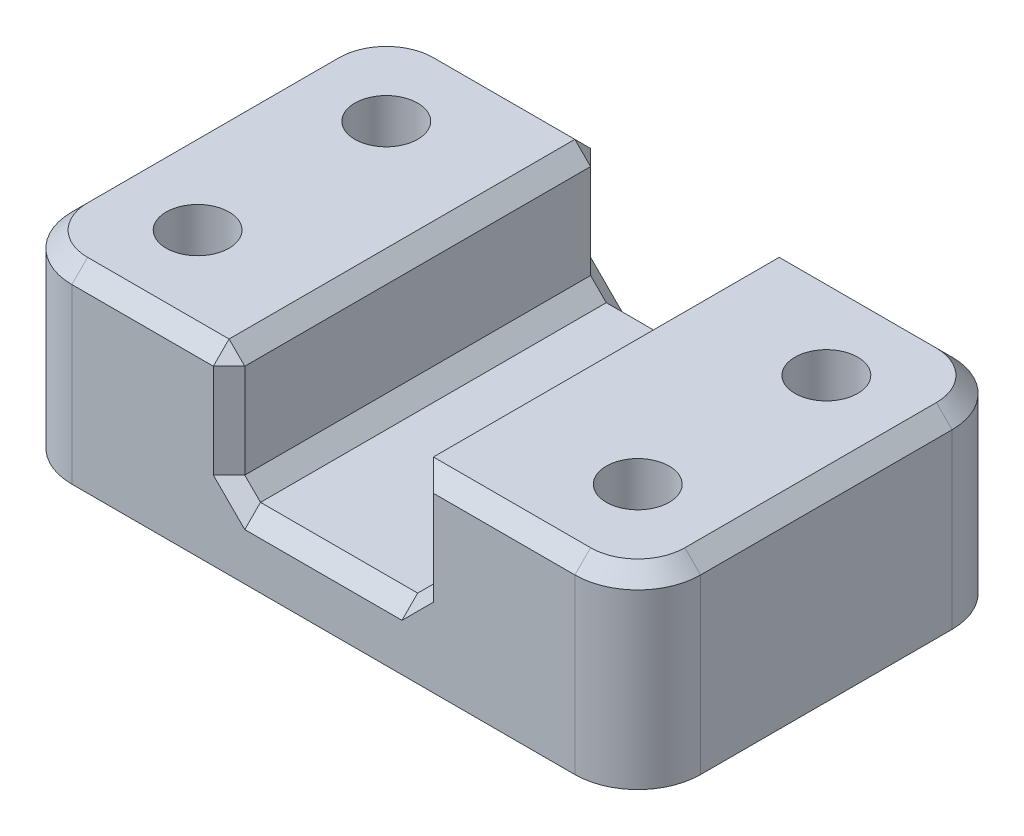
SolidWorks part; units mm, degrees
ref_plane "Front Plane" through (0, 0, 0) normal (0, 0, 1) x (1, 0, 0)
ref_plane "Top Plane" through (0, 0, 0) normal (0, 1, 0) x (1, 0, 0)
ref_plane "Right Plane" through (0, 0, 0) normal (1, 0, 0) x (0, 0, -1)
sketch "Sketch2" plane through (0, 0, 0) normal (0, 1, 0) x (1, 0, 0)
  line L0 (0, 23.318) -> (0, 0) construction
  line L1 (-63.5, -38.1) -> (63.5, -38.1)
  line L2 (-63.5, -38.1) -> (-63.5, 38.1)
  line L3 (-63.5, 38.1) -> (63.5, 38.1)
  line L4 (63.5, -38.1) -> (63.5, 38.1)
  line L5 (-63.5, -38.1) -> (63.5, 38.1) construction
  line L6 (-63.5, 38.1) -> (63.5, -38.1) construction
  line L7 (0, 0) -> (-53.7148, 0) construction
  circle A0 centre (-44.45, 19.05) radius 6.35
  circle A1 centre (44.45, 19.05) radius 6.35
  circle A2 centre (-44.45, -19.05) radius 6.35
  circle A3 centre (44.45, -19.05) radius 6.35
  point P0 (0, 0)
  dimension "D3" = 12.7
  dimension "D1" = 127
  dimension "D2" = 76.2
  dimension "D4" = 19.05
  dimension "D5" = 19.05
extrude "Boss-Extrude1" add sketch "Sketch2" along normal blind 38.1
sketch "Sketch3" plane through (0, 38.1, 0) normal (0, 1, 0) x (1, 0, 0)
  line L0 (63.5, 38.1) -> (-63.5, 38.1) construction
  line L1 (-19.05, -38.1) -> (19.05, -38.1)
  line L2 (-19.05, -38.1) -> (-19.05, 38.1)
  line L3 (-19.05, 38.1) -> (19.05, 38.1)
  line L4 (19.05, -38.1) -> (19.05, 38.1)
  line L5 (-19.05, -38.1) -> (19.05, 38.1) construction
  line L6 (-19.05, 38.1) -> (19.05, -38.1) construction
  point P0 (0, 0)
  point P8 (0, 0)
  point P9 (0, 0)
  dimension "D1" = 38.1
extrude "Cut-Extrude2" cut sketch "Sketch3" against normal blind 25.4 contours L2 L1 L4 L3
fillet "Fillet1" radius 12.7 4 edges at (-63.5, 19.05, -38.1) (-63.5, 19.05, 38.1) (63.5, 19.05, -38.1) (63.5, 19.05, 38.1)
chamfer "Chamfer1" distance 3.175 angle 45 19 edges at (-19.05, 38.1, 0) (-34.925, 38.1, 38.1) (-59.7803, 38.1, 34.3803) (-63.5, 38.1, 0) (-59.7803, 38.1, -34.3803) (-34.925, 38.1, -38.1) (19.05, 25.4, 38.1) (19.05, 25.4, -38.1) (-19.05, 25.4, 38.1) (-19.05, 25.4, -38.1) (19.05, 12.7, 0) (0, 12.7, 38.1) (-19.05, 12.7, 0) (0, 12.7, -38.1) (34.925, 38.1, -38.1) (59.7803, 38.1, -34.3803) (63.5, 38.1, 0) (59.7803, 38.1, 34.3803) (34.925, 38.1, 38.1)
